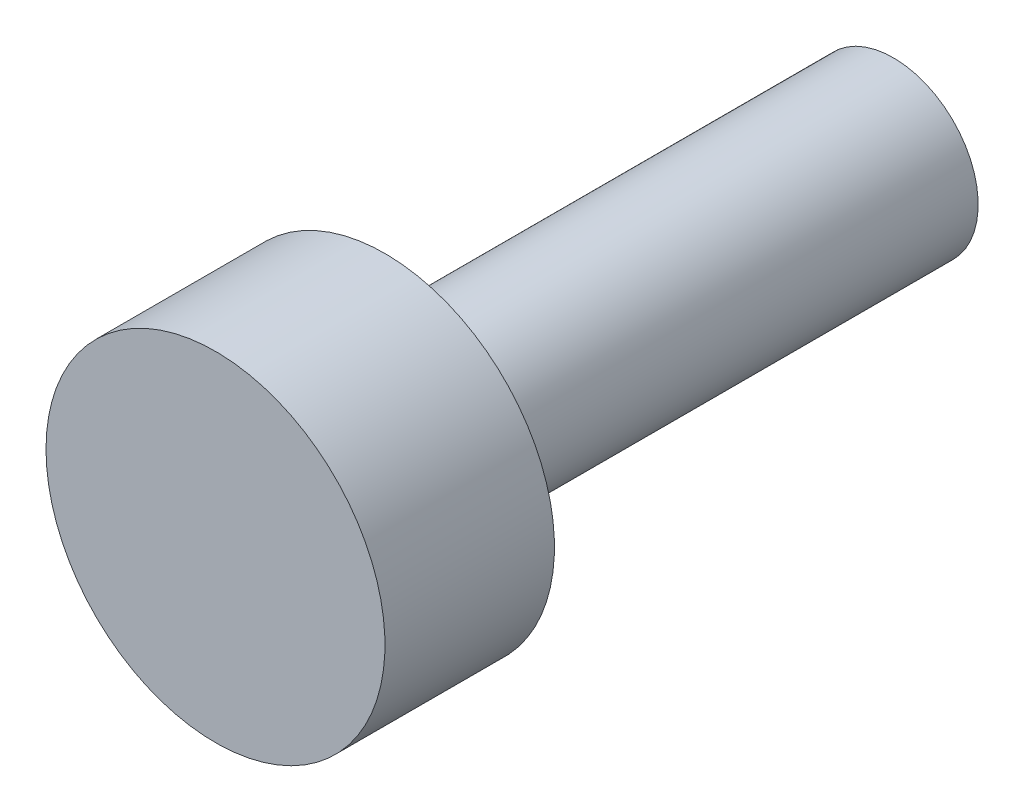
SolidWorks part; units mm, degrees
ref_plane "Front Plane" through (0, 0, 0) normal (0, 0, 1) x (1, 0, 0)
ref_plane "Top Plane" through (0, 0, 0) normal (0, 1, 0) x (1, 0, 0)
ref_plane "Right Plane" through (0, 0, 0) normal (1, 0, 0) x (0, 0, -1)
sketch "Croquis1" plane through (0, 0, 0) normal (0, 1, 0) x (1, 0, 0)
  line L0 (0, 8.5326) -> (0, -11.4674)
  line L1 (0, -11.4674) -> (-5, -11.4674)
  line L2 (-5, -11.4674) -> (-5, -6.4674)
  line L3 (-5, -6.4674) -> (-2.5, -6.4674)
  line L4 (-2.5, -6.4674) -> (-2.5, 8.5326)
  line L5 (-2.5, 8.5326) -> (0, 8.5326)
  dimension "D1" = 15
  dimension "D2" = 5
  dimension "D3" = 5
  dimension "D4" = 2.5
revolve "Revolución1" add sketch "Croquis1" angle 360 about L0
